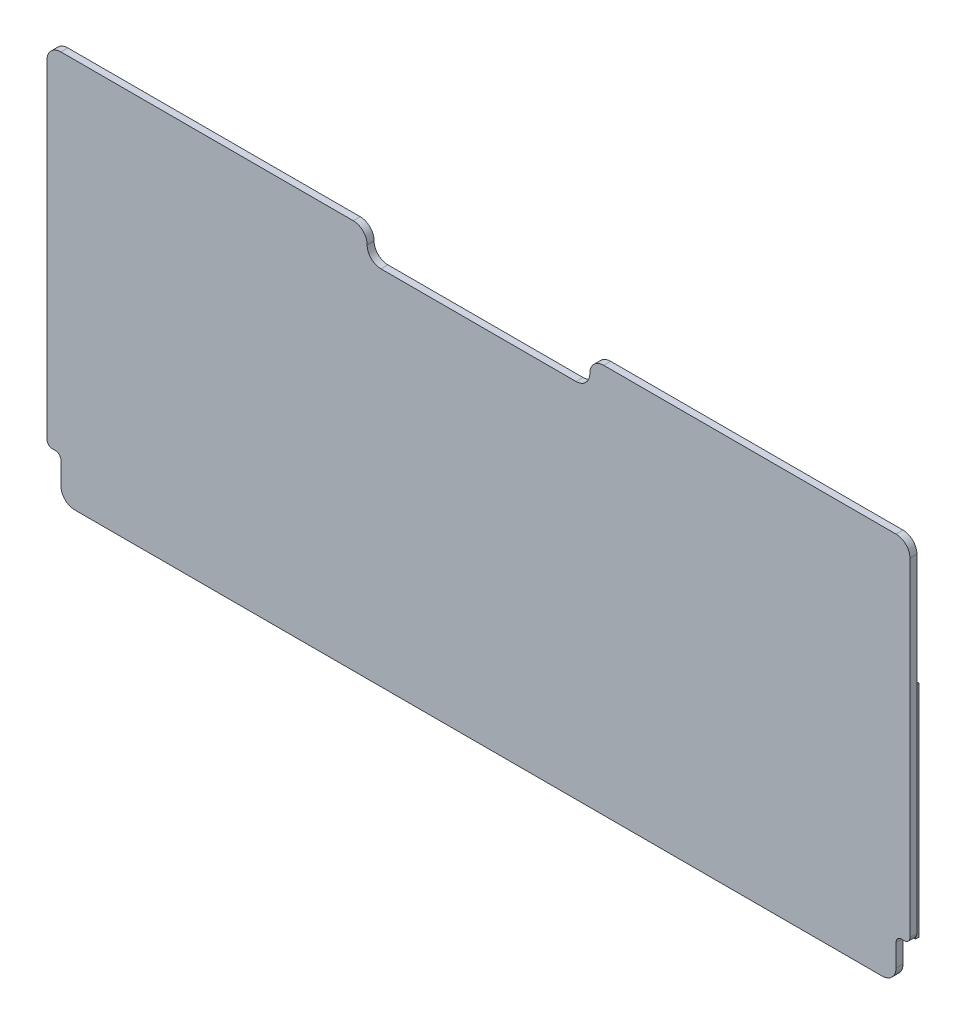
SolidWorks part; units mm, degrees
material "Polyester Resin"
ref_plane "Front Plane" through (0, 0, 0) normal (0, 0, 1) x (1, 0, 0)
ref_plane "Top Plane" through (0, 0, 0) normal (0, 1, 0) x (1, 0, 0)
ref_plane "Right Plane" through (0, 0, 0) normal (1, 0, 0) x (0, 0, -1)
sketch "Sketch1" plane through (0, 0, 0) normal (0, 0, 1) x (1, 0, 0)
  line L0 (-50.8, 171.5098) -> (-50.8, 171.3902)
  line L1 (-190.5, 177.8) -> (-57.0902, 177.8)
  line L2 (-196.85, 171.45) -> (-196.85, 21.59)
  line L3 (-184.15, 0) -> (184.15, 0)
  line L4 (196.85, 171.45) -> (196.85, 21.59)
  line L5 (57.0902, 177.8) -> (190.5, 177.8)
  line L6 (-44.5098, 165.1) -> (44.5098, 165.1)
  line L7 (50.8, 171.3902) -> (50.8, 171.5098)
  line L8 (0, -55) -> (0, 55) construction
  line L9 (-194.31, 19.05) -> (-193.04, 19.05)
  line L10 (-190.5, 16.51) -> (-190.5, 6.35)
  line L11 (194.31, 19.05) -> (193.04, 19.05)
  line L12 (190.5, 16.51) -> (190.5, 6.35)
  arc A1 (-50.8, 171.3902) -> (-44.5098, 165.1) centre (-44.5098, 171.3902) ccw
  arc A3 (-50.8, 171.5098) -> (-57.0902, 177.8) centre (-57.0902, 171.5098) ccw
  arc A4 (44.5098, 165.1) -> (50.8, 171.3902) centre (44.5098, 171.3902) ccw
  arc A5 (57.0902, 177.8) -> (50.8, 171.5098) centre (57.0902, 171.5098) ccw
  arc A8 (196.85, 171.45) -> (190.5, 177.8) centre (190.5, 171.45) ccw
  arc A9 (-196.85, 171.45) -> (-190.5, 177.8) centre (-190.5, 171.45) cw
  arc A10 (194.31, 19.05) -> (196.85, 21.59) centre (194.31, 21.59) ccw
  arc A11 (193.04, 19.05) -> (190.5, 16.51) centre (193.04, 16.51) ccw
  arc A12 (-193.04, 19.05) -> (-190.5, 16.51) centre (-193.04, 16.51) cw
  arc A13 (-194.31, 19.05) -> (-196.85, 21.59) centre (-194.31, 21.59) cw
  arc A14 (184.15, 0) -> (190.5, 6.35) centre (184.15, 6.35) ccw
  arc A15 (-190.5, 6.35) -> (-184.15, 0) centre (-184.15, 6.35) ccw
  point P22 (196.85, 19.05)
  point P23 (196.85, 0)
  point P26 (196.85, 177.8)
  point P29 (-196.85, 177.8)
  point P35 (190.5, 19.05)
  point P38 (-190.5, 19.05)
  point P41 (-196.85, 19.05)
  point P44 (190.5, 0)
  point P47 (-190.5, 0)
  dimension "D3" = 12.7
  dimension "D4" = 50.8
  dimension "D6" = 12.5804
  dimension "D7" = 6.35
  dimension "D10" = 2.54
  dimension "D1" = 393.7
  dimension "D2" = 177.8
  dimension "D5" = 50.8
  dimension "D8" = 19.05
  dimension "D9" = 6.35
extrude "Boss-Extrude1" add sketch "Sketch1" along normal blind 3.175
sketch "Sketch2" plane through (0, 0, 0) normal (0, 0, -1) x (-1, 0, 0)
  line L0 (-196.215, 19.05) -> (-196.215, 119.38)
  line L5 (-196.215, 119.38) -> (-184.785, 119.38)
  line L6 (-184.785, 119.38) -> (-184.785, 19.05)
  line L7 (-184.785, 19.05) -> (-196.215, 19.05)
  line L16 (-196.85, 21.59) -> (-196.85, 171.45) construction
  line L17 (55, 0) -> (-55, 0) construction
  line L18 (0, 55) -> (0, -55) construction
  line L19 (184.785, 19.05) -> (196.215, 19.05)
  line L20 (184.785, 119.38) -> (184.785, 19.05)
  line L21 (196.215, 119.38) -> (184.785, 119.38)
  line L22 (196.215, 19.05) -> (196.215, 119.38)
  dimension "D1" = 11.43
  dimension "D2" = 100.33
  dimension "D3" = 0.635
  dimension "D4" = 19.05
extrude "Boss-Extrude2" add sketch "Sketch2" along normal blind 1.5875
